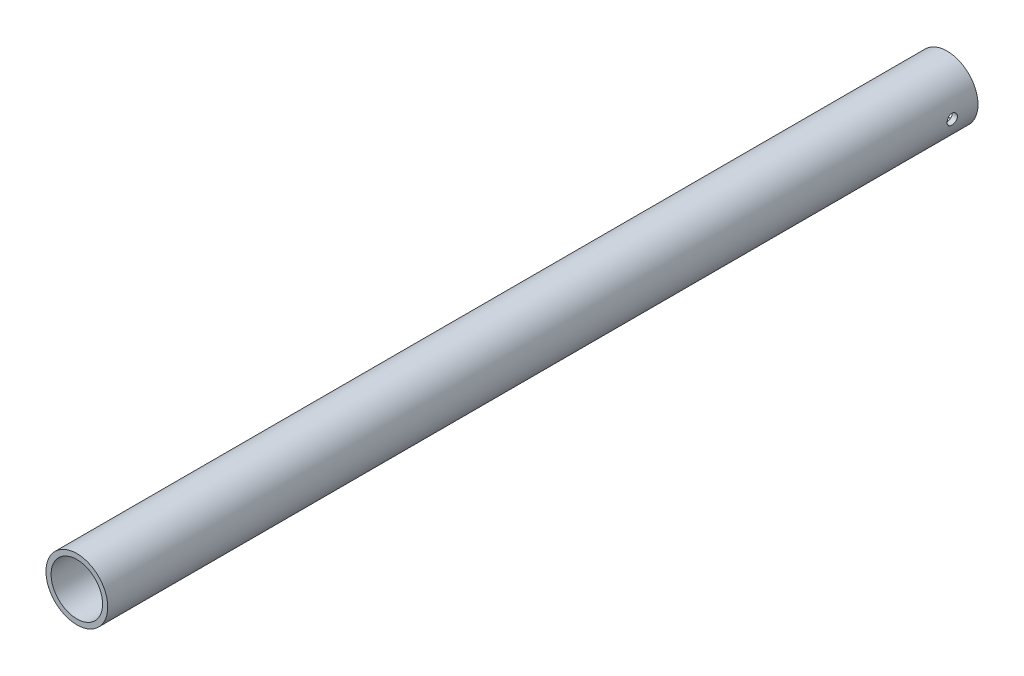
SolidWorks part; units mm, degrees
ref_plane "Ön Düzlem" through (0, 0, 0) normal (0, 0, 1) x (1, 0, 0)
ref_plane "Üst Düzlem" through (0, 0, 0) normal (0, 1, 0) x (1, 0, 0)
ref_plane "Sağ Düzlem" through (0, 0, 0) normal (1, 0, 0) x (0, 0, -1)
sketch "Sketch1" plane through (0, 0, 0) normal (0, 0, 1) x (1, 0, 0)
  circle A0 centre (0, 0) radius 6
  circle A1 centre (0, 0) radius 5
  dimension "D1" = 10
  dimension "D2" = 1
extrude "Boss-Extrude1" add sketch "Sketch1" along normal blind 169
sketch "Çizim1" plane through (0, 0, 0) normal (1, 0, 0) x (0, 0, -1)
  circle A0 centre (-5, 0) radius 1
  dimension "D2" = 2
  dimension "D1" = 5
extrude "Kes-Ekstrüzyon1" cut sketch "Çizim1" against normal through all both and the other way through all
